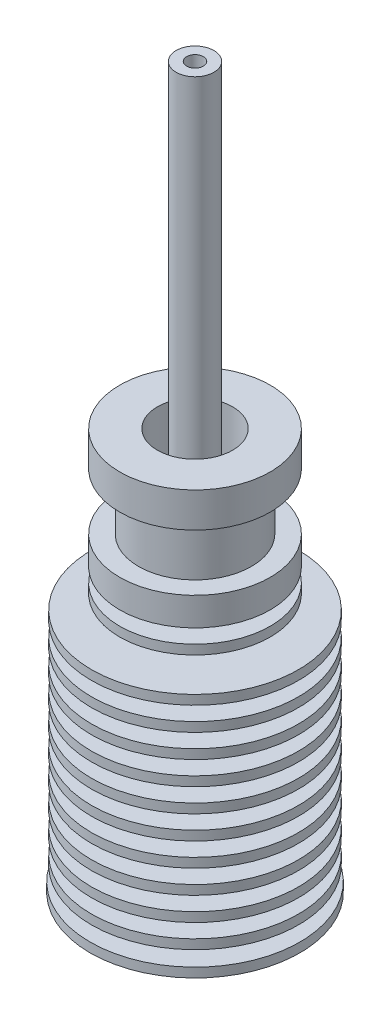
SolidWorks part; units mm, degrees
material "6061 Alloy"
ref_plane "Front Plane" through (0, 0, 0) normal (0, 0, 1) x (1, 0, 0)
ref_plane "Top Plane" through (0, 0, 0) normal (0, 1, 0) x (1, 0, 0)
ref_plane "Right Plane" through (0, 0, 0) normal (1, 0, 0) x (0, 0, -1)
sketch "Sketch1" plane through (0, 0, 0) normal (0, 0, 1) x (1, 0, 0)
  line L0 (0, 0) -> (0, -50000) construction
  line L1 (0, 0) -> (11.15, 0)
  line L2 (11.15, 0) -> (11.15, 1)
  line L3 (8, 30) -> (3.5, 30)
  line L4 (8, 30) -> (8, 33)
  line L5 (8, 33) -> (6, 33)
  line L6 (6, 33) -> (6, 39)
  line L7 (6, 39) -> (8, 39)
  line L8 (8, 39) -> (8, 42.7)
  line L9 (8, 42.7) -> (0, 42.7)
  line L10 (0, 42.7) -> (0, 0)
  line L12 (11, 1) -> (11, 26)
  line L13 (3.5, 26) -> (11, 26)
  line L14 (3.5, 27.5) -> (8, 27.5)
  line L15 (8, 27.5) -> (8, 28.5)
  line L16 (8, 28.5) -> (3.5, 28.5)
  line L17 (3.5, 28.5) -> (3.5, 30)
  line L18 (3.5, 27.5) -> (3.5, 26)
  line L20 (11.15, 1) -> (11, 1)
  dimension "D1" = 22.3
  dimension "D2" = 16
  dimension "D3" = 12
  dimension "D4" = 16
  dimension "D5" = 3.7
  dimension "D6" = 6
  dimension "D7" = 3
  dimension "D8" = 42.7
  dimension "D9" = 26
  dimension "D10" = 1.5
  dimension "D11" = 1
  dimension "D12" = 7
  dimension "D13" = 22
  dimension "D14" = 1
revolve "Revolve1" add sketch "Sketch1" angle 360 about L0
sketch "Sketch2" plane through (0, 0, 0) normal (0, 0, 1) x (1, 0, 0)
  line L0 (11, 1) -> (11, 26) construction
  line L3 (11, 1) -> (6, 1)
  line L4 (6, 1) -> (6, 2.5)
  line L5 (6, 2.5) -> (11, 2.5)
  line L6 (0, 0) -> (0, 26) construction
  line L7 (11.15, 26) -> (-11.15, 26) construction
  line L8 (11, 2.5) -> (11, 1)
  dimension "D1" = 2.5
  dimension "D3" = 12
revolve "Cut-Revolve1" cut sketch "Sketch2" angle 360 about L6
pattern_linear "LPattern1" count 10 spacing 2.5 along (0, 1, 0) of "Cut-Revolve1"
sketch "Sketch3" plane through (0, 0, 0) normal (0, 0, 1) x (1, 0, 0)
  line L0 (0, 42.7) -> (0, 0)
  line L1 (8, 42.7) -> (-8, 42.7) construction
  line L2 (0, 0) -> (2.1, 0)
  line L3 (-11.15, 0) -> (11.15, 0) construction
  line L4 (2.1, 0) -> (2.1, 34.3)
  line L6 (4, 36.2) -> (4, 42.7)
  line L7 (4, 42.7) -> (0, 42.7)
  line L8 (4, 36.2) -> (2.1, 34.3)
  dimension "D1" = 4
  dimension "D2" = 2.1
  dimension "D3" = 6.5
  dimension "D4" = 45
revolve "Cut-Revolve2" cut sketch "Sketch3" angle 360 about L0
hole_wizard "M7x1.0 Tapped Hole1" positions "Sketch5" profile "Sketch4" tap size "M7x1.0" standard "ANSI Metric"
sketch "Sketch5" plane through (0, 0, 0) normal (0, -1, 0) x (-1, 0, 0)
  point P0 (0, 0)
sketch "Sketch4" plane through (0, 0, 0) normal (1, 0, 0) x (0, 0, -1)
  line L0 (0, 0) -> (0, 16.9026)
  line L1 (0, 16.9026) -> (3, 15.1)
  line L2 (3, 15.1) -> (3, 0)
  line L5 (3, 0) -> (0, 0)
  line L10 (0, 16.9026) -> (-3, 15.1) construction
  line L11 (0, -6.35) -> (0, 107.95) construction
  dimension "Tap Drill Dia." = 6
  dimension "Tap Drill Depth" = 15.1
  dimension "Drill Angle" = 118
cosmetic thread "Hole Thread1" parameters "D1"=14, "D2"=7
sketch "Sketch6" plane through (0, 0, 0) normal (0, 0, 1) x (1, 0, 0)
  line L0 (0, 0) -> (0, 42.7) construction
  line L1 (0, 33) -> (0, 39) construction
  line L2 (4, 42.7) -> (-4, 42.7) construction
  line L3 (0.885, 36) -> (2.005, 36)
  line L4 (0.885, 36) -> (0.885, 76.4966)
  line L5 (0.885, 76.4966) -> (2.005, 76.4966)
  line L6 (2.005, 36) -> (2.005, 76.4966)
  line L7 (1.445, 76.4966) -> (1.445, 36) construction
  line L8 (0.885, 56.2483) -> (2.005, 56.2483) construction
  point P9 (0, 42.7)
  point P337 (1.445, 56.2483)
  dimension "D1" = 1.77
  dimension "D2" = 4.01
  dimension "D3" = 36
revolve "Revolve2" add sketch "Sketch6" angle 360 about L0
